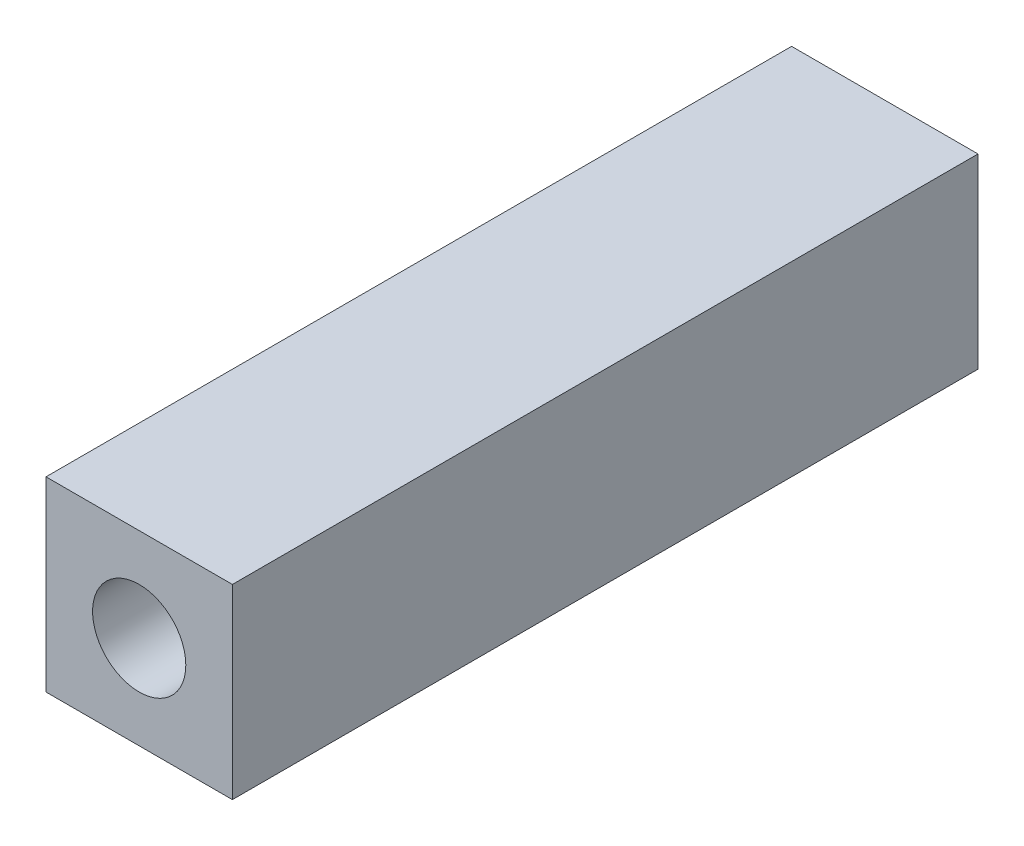
SolidWorks part; units mm, degrees
ref_plane "Front Plane" through (0, 0, 0) normal (0, 0, 1) x (1, 0, 0)
ref_plane "Top Plane" through (0, 0, 0) normal (0, 1, 0) x (1, 0, 0)
ref_plane "Right Plane" through (0, 0, 0) normal (1, 0, 0) x (0, 0, -1)
sketch "Sketch1" plane through (0, 0, 0) normal (0, 0, 1) x (1, 0, 0)
  line L1 (-5, 5) -> (5, 5)
  line L2 (-5, 5) -> (-5, -5)
  line L3 (-5, -5) -> (5, -5)
  line L4 (5, 5) -> (5, -5)
  line L5 (-5, 5) -> (5, -5) construction
  line L6 (-5, -5) -> (5, 5) construction
  circle A0 centre (0, 0) radius 2.5
  point P0 (0, 0)
  dimension "D3" = 5
  dimension "D1" = 10
  dimension "D2" = 10
extrude "Boss-Extrude1" add sketch "Sketch1" along normal blind 40
